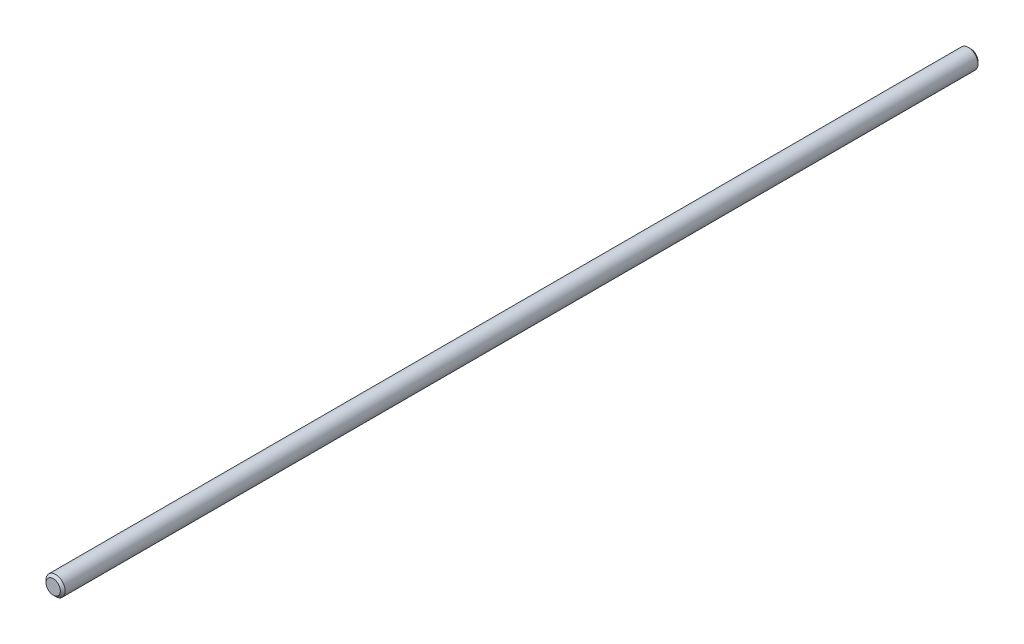
SolidWorks part; units mm, degrees
material "1060 Alloy"
ref_plane "Front" through (0, 0, 0) normal (0, 0, 1) x (1, 0, 0)
ref_plane "Top" through (0, 0, 0) normal (0, 1, 0) x (1, 0, 0)
ref_plane "Right" through (0, 0, 0) normal (1, 0, 0) x (0, 0, -1)
sketch "Sketch1" plane through (0, 0, 0) normal (0, 0, 1) x (1, 0, 0)
  circle A0 centre (0, 0) radius 3.9688
  dimension "D1" = 7.9375
extrude "Boss-Extrude1" add sketch "Sketch1" along normal blind 380
chamfer "Chamfer2" distance 1 angle 45 1 edges at (3.9688, 0, 0)
chamfer "Chamfer3" distance 1 angle 45 1 edges at (3.9688, 0, 380)
